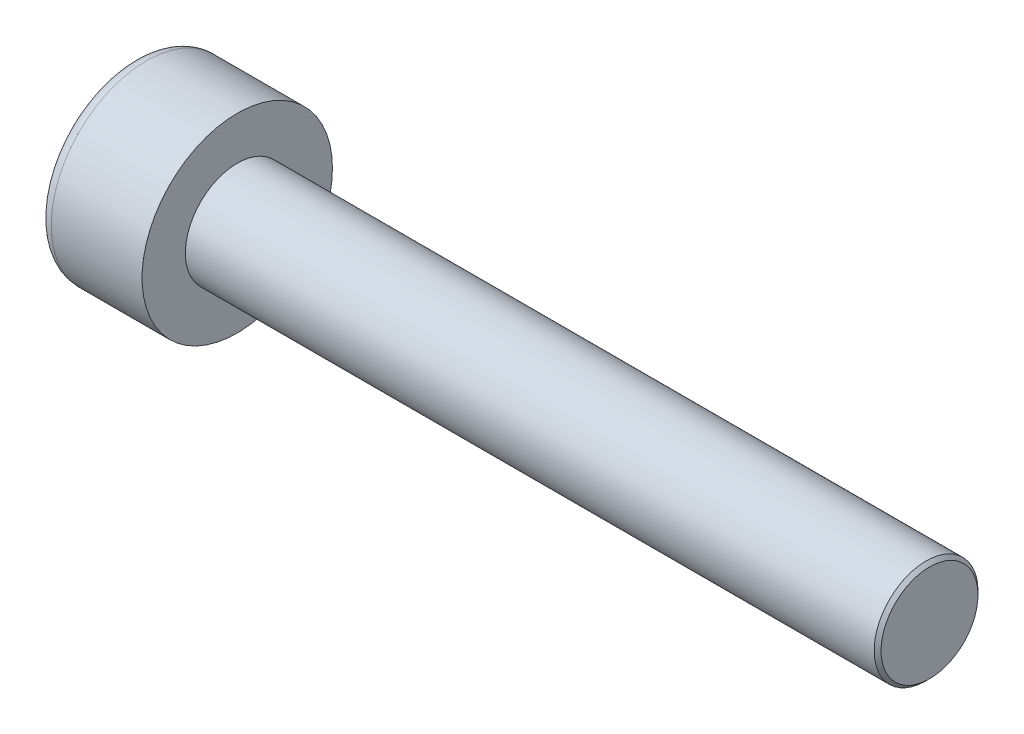
SolidWorks part; units mm, degrees
ref_plane "Front" through (0, 0, 0) normal (0, 0, 1) x (1, 0, 0)
ref_plane "Top" through (0, 0, 0) normal (0, 1, 0) x (1, 0, 0)
ref_plane "Right" through (0, 0, 0) normal (1, 0, 0) x (0, 0, -1)
sketch "Sketch1" plane through (0, 0, 0) normal (1, 0, 0) x (0, 0, -1)
  circle A0 centre (0, 0) radius 2.75
  dimension "dk" = 5.5
extrude "BaseHead" add sketch "Sketch1" along normal blind 3
sketch "Sketch2" plane through (3, 0, 0) normal (1, 0, 0) x (0, 0, -1)
  circle A0 centre (0, 0) radius 1.5
  dimension "d" = 3
extrude "BaseBody" add sketch "Sketch2" along normal blind 20
cosmetic thread "ThreadCosmetic1" parameters "b"=10, "D2"=2.459
sketch "Sketch3" plane through (0, 0, 0) normal (1, 0, 0) x (0, 0, -1)
  line L1 (1.4434, 0) -> (0.7217, 1.25)
  line L2 (0.7217, 1.25) -> (-0.7217, 1.25)
  line L3 (-0.7217, 1.25) -> (-1.4434, 0)
  line L4 (-1.4434, 0) -> (-0.7217, -1.25)
  line L5 (-0.7217, -1.25) -> (0.7217, -1.25)
  line L6 (0.7217, -1.25) -> (1.4434, 0)
  circle A0 centre (0, 0) radius 1.25 construction
  dimension "s" = 2.5
  dimension "e" = 2.8868
extrude "HexagonSocket" cut sketch "Sketch3" along normal blind 1.3
sketch "Sketch4" plane through (-4.1961, 0.75, 0) normal (0, 0, 1) x (-1, 0, 0)
  line L0 (-5.4961, 2) -> (-6.2178, 0.75)
  line L2 (-6.2178, 0.75) -> (-5.4961, 0.75)
  line L3 (-5.4961, 0.75) -> (-5.4961, 2)
  line L4 (-5.0351, 0.75) -> (0.839, 0.75) construction
  line L5 (-27.1961, 0.75) -> (-7.1961, 0.75) construction
  line L6 (-7.1961, 0.75) -> (-4.1961, 0.75) construction
  dimension "m" = 60
revolve "Cut-Revolve1" cut sketch "Sketch4" angle 360 about L4
fillet "HeadFillet" [suppressed] radius 0.1
fillet "TopFillet" radius 0.375 1 edges at (0, 0, -2.75)
chamfer "Chamfer1" distance 0.1 angle 45 1 edges at (23, 0, -1.5)
sketch "Sketch5" plane through (0, 0, 0) normal (0, 0, 1) x (1, 0, 0)
  line L0 (22.9, 1.2657) -> (23.0353, 1.5)
  line L1 (23.0353, 1.5) -> (23.0353, 1.7705)
  line L2 (23.0353, 1.7705) -> (22.7648, 1.7705)
  line L3 (22.7648, 1.7705) -> (22.7648, 1.5)
  line L4 (22.7648, 1.5) -> (22.9, 1.2657)
  line L5 (0, 0) -> (7.8886, 0) construction
  line L6 (22.9, -1.5) -> (22.9, 1.5) construction
  dimension "D1" = 3
  dimension "D2" = 0.2705
revolve "Cut-Revolve10" [suppressed] cut sketch "Sketch5" angle 360 about L5
pattern_linear "LPattern10" [suppressed] count 31 spacing 0.3246 along (1, 0, 0)
equation "\"r1@TopFillet\" = \"d@Sketch2\" / 8"
equation "\"D1@Chamfer1\" = \"r@HeadFillet\""
equation "\"D1@Sketch5\" = \"d@Sketch2\""
equation "\"D2@Sketch5\" =  ( \"d@Sketch2\" - \"D2@ThreadCosmetic1\" )  / 2"
equation "\"D3@LPattern10\" = \"D2@Sketch5\" * 1.2"
equation "\"D1@LPattern10\" = \"b@ThreadCosmetic1\" / \"D3@LPattern10\""
